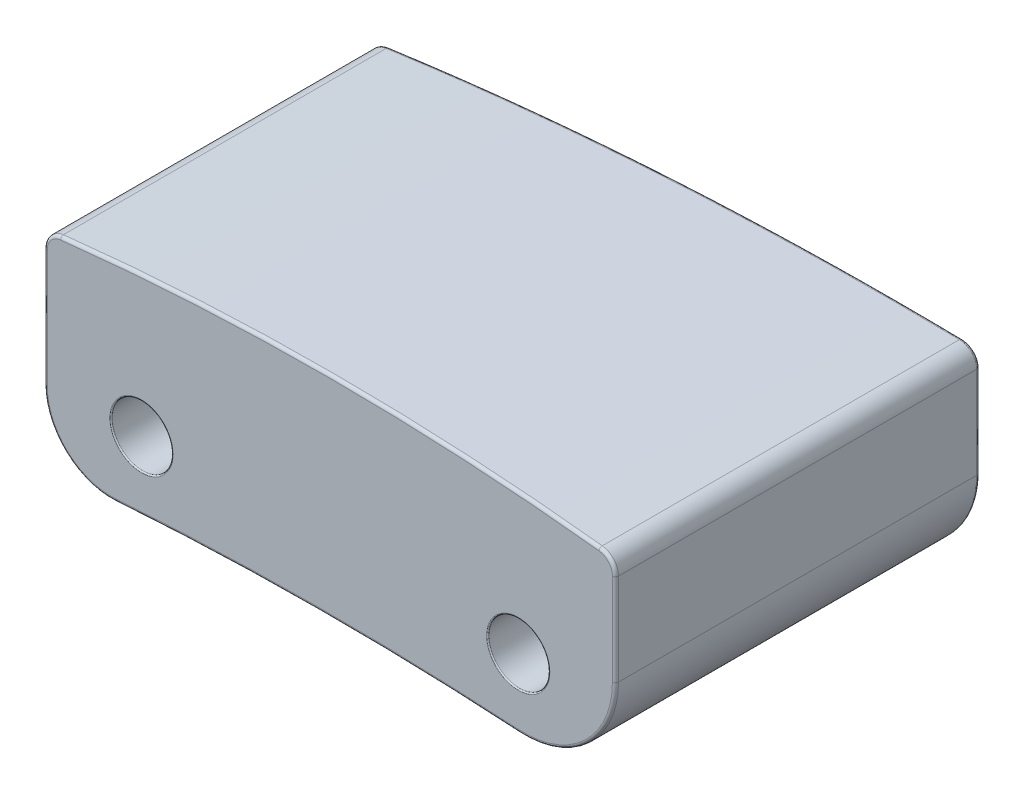
SolidWorks part; units mm, degrees
ref_plane "Front Plane" through (0, 0, 0) normal (0, 0, 1) x (1, 0, 0)
ref_plane "Top Plane" through (0, 0, 0) normal (0, 1, 0) x (1, 0, 0)
ref_plane "Right Plane" through (0, 0, 0) normal (1, 0, 0) x (0, 0, -1)
sketch "Sketch1" plane through (0, 0, 0) normal (0, 0, 1) x (1, 0, 0)
  line L0 (55, 0) -> (-55, 0) construction
  line L1 (-4.7, 1.85) -> (4.7, 1.85)
  line L2 (-4.7, 1.85) -> (-4.7, -1.85)
  line L3 (-4.7, -1.85) -> (4.7, -1.85)
  line L4 (4.7, 1.85) -> (4.7, -1.85)
  line L5 (0, -55) -> (0, 55) construction
  dimension "D1" = 9.4
  dimension "D2" = 3.7
  dimension "D3" = 1.85
  dimension "D4" = 4.7
extrude "Boss-Extrude1" add sketch "Sketch1" along normal mid plane 6
sketch "Sketch2" plane through (0, 0, 3) normal (0, 0, 1) x (1, 0, 0)
  line L0 (-4.7, 1.85) -> (-4.7, -1.85) construction
  line L1 (4.7, -1.85) -> (4.7, 1.85) construction
  line L2 (-4.7, -1.85) -> (4.7, -1.85) construction
  line L3 (4.7, 1.85) -> (-4.7, 1.85) construction
  line L4 (-4.7, 1.55) -> (-7.1207, 4.0114)
  line L5 (-7.1207, 4.0114) -> (5.5359, 3.8867)
  line L6 (5.5359, 3.8867) -> (4.7, 1.55)
  line L7 (4.7, -1.85) -> (0.3506, -3.782)
  line L8 (-4.7, -1.85) -> (0.3506, -3.782)
  arc A0 (-4.7, 1.55) -> (4.7, 1.55) centre (0, -38.1729) cw
  arc A1 (-4.7, -1.85) -> (4.7, -1.85) centre (0, -51.6286) cw
  dimension "D4" = 40
  dimension "D5" = 50
  dimension "D1" = 0
  dimension "D2" = 0.3
  dimension "D3" = 0.3
extrude "Cut-Extrude1" cut sketch "Sketch2" against normal blind 15.6
fillet "Fillet1" radius 1.1 1 edges at (-4.7, -1.85, 0)
fillet "Fillet6" radius 1.5 1 edges at (4.7, -1.85, 0)
fillet "Fillet2" radius 0.3 2 edges at (4.7, 1.55, 0) (-4.7, 1.55, 0)
sketch "Sketch3" plane through (0, 0, 3) normal (0, 0, 1) x (1, 0, 0)
  line L0 (0, -1.9705) -> (0, 1.9705) construction
  line L1 (3.3, 0) -> (-3.3, 0) construction
  circle A0 centre (3.1, -0.6) radius 0.5
  circle A1 centre (-3.1, -0.6) radius 0.5
  dimension "D1" = 1
  dimension "D3" = 1
  dimension "D4" = 3.1
  dimension "D5" = 0.6
  dimension "D6" = 0.6
  dimension "D2" = 3.1
extrude "Cut-Extrude2" cut sketch "Sketch3" against normal blind 3
sketch "Sketch4" plane through (0, 0, 0) normal (0, 1, 0) x (1, 0, 0)
  line L0 (-4.4332, -3) -> (4.4332, -3) construction
  line L1 (4.7, 3) -> (4.7, -3) construction
  line L2 (-4.7, -3) -> (-4.7, 3) construction
  line L4 (-4.7, 2.4) -> (-6.6127, 4.1139)
  line L5 (-6.6127, 4.1139) -> (6.4207, 4.9741)
  line L6 (6.4207, 4.9741) -> (4.7, 3)
  arc A0 (4.7, 3) -> (-4.7, 2.4) centre (-9.5503, 152.3216) cw
  dimension "D5" = 150
  dimension "D1" = 0
  dimension "D2" = 0
  dimension "D3" = 5.4
  dimension "D4" = 6
extrude "Cut-Extrude3" cut sketch "Sketch4" against normal mid plane 10
fillet "Fillet5" radius 0.05 17 edges at (4.7, 0.5272, 3) (-0.2083, -1.629, 3) (-4.3499, -1.4603, 3) (-4.7, 0.3135, 3) (-4.7, 0.3135, -2.4) (-4.2253, -1.5605, -2.4161) (4.7, 0.5272, -3) (4.6127, 1.494, -2.9917) (3.6, -0.6, 0) (0, 1.8271, 3) (-4.6236, 1.4825, 3) (4.6236, 1.4825, 3) (-4.6343, 1.4698, -2.4021) (4.2272, -1.3212, 3) (4.3738, -1.1621, -2.9692)
sketch "Sketch5" plane through (0, 0, 0) normal (0, 1, 0) x (1, 0, 0)
  line L0 (-3.526, -3) -> (3.1099, -3) construction
  line L1 (-4.7, 2.3516) -> (-4.7, -2.95) construction
  circle A0 centre (-0.7, -1.5) radius 0.4
  dimension "D1" = 1.5
  dimension "D2" = 4
  dimension "D3" = 0.8
extrude "Cut-Extrude5" cut sketch "Sketch5" along normal offset from surface (8.7665 mm away) 0.4 from offset 10 offset against normal yes
fillet "Fillet7" radius 0.05 1 edges at (-0.792, -1.6349, 1.8893)
fillet "Fillet8" radius 0.02 2 edges at (3.6, -0.6, 3) (-2.6, -0.6, 3)
